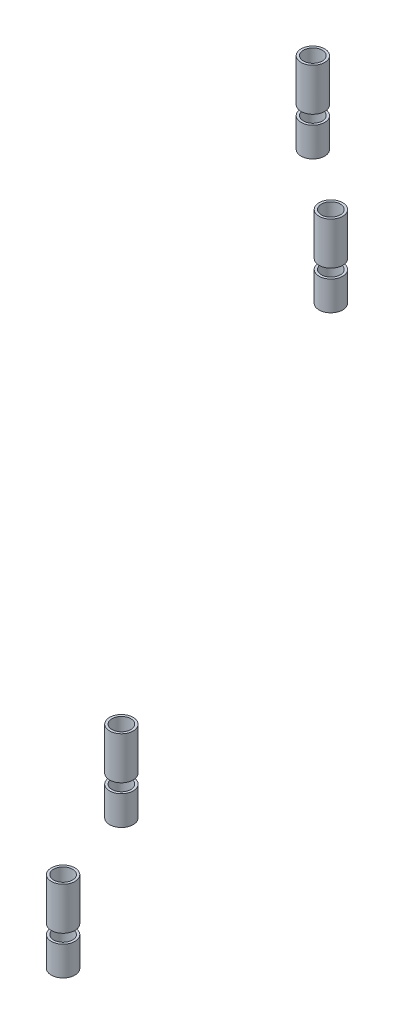
SolidWorks part; units mm, degrees
material "ABS"
ref_plane "Płaszczyzna XY" through (0, 0, 0) normal (0, 0, 1) x (1, 0, 0)
ref_plane "Płaszczyzna XZ" through (0, 0, 0) normal (0, 1, 0) x (1, 0, 0)
ref_plane "Płaszczyzna YZ" through (0, 0, 0) normal (1, 0, 0) x (0, 0, -1)
sketch "Szkic1" plane through (0, 472.5, 0) normal (0, -1, 0) x (1, 0, 0)
  circle A0 centre (-209.2942, 235.2328) radius 2 construction
  circle A1 centre (-85.5135, 411.9205) radius 2 construction
  circle A2 centre (-106.9414, 378.1441) radius 2 construction
  circle A3 centre (-209.2942, 235.2328) radius 2
  circle A4 centre (-85.5135, 411.9205) radius 2
  circle A5 centre (-106.9414, 378.1441) radius 2
  circle A6 centre (-179.1662, 261.5446) radius 2 construction
  circle A7 centre (-179.1662, 261.5446) radius 2
  circle A8 centre (-209.2942, 235.2328) radius 2.5
  circle A9 centre (-179.1662, 261.5446) radius 2.5
  circle A10 centre (-106.9414, 378.1441) radius 2.5
  circle A11 centre (-85.5135, 411.9205) radius 2.5
  dimension "D1" = 5
  dimension "D2" = 5
  dimension "D3" = 5
  dimension "D4" = 5
extrude "Dodanie-wyciągnięcie1" add sketch "Szkic1" along normal up to surface (9 mm away)
sketch "Szkic2" plane through (0, 461.5, 0) normal (0, -1, 0) x (1, 0, 0)
  circle A0 centre (-209.2942, 235.2328) radius 2.5 construction
  circle A1 centre (-209.2942, 235.2328) radius 2.5
  circle A2 centre (-209.2942, 235.2328) radius 2
  circle A3 centre (-179.1662, 261.5446) radius 2.5
  circle A4 centre (-179.1662, 261.5446) radius 2
  circle A5 centre (-106.9414, 378.1441) radius 2
  circle A6 centre (-106.9414, 378.1441) radius 2.5
  circle A7 centre (-85.5135, 411.9205) radius 2
  circle A8 centre (-85.5135, 411.9205) radius 2.5
extrude "Dodanie-wyciągnięcie2" add sketch "Szkic2" along normal up to surface (6.2 mm away) separate body
